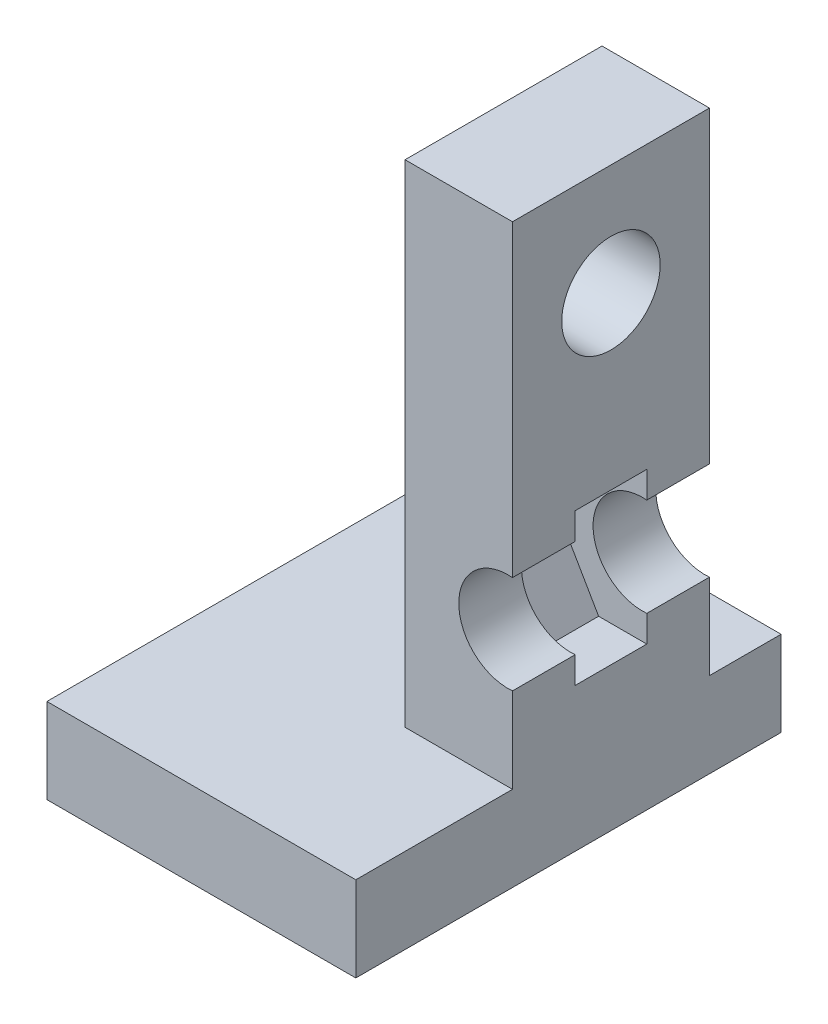
SolidWorks part; units mm, degrees
ref_plane "前基準面" through (0, 0, 0) normal (0, 0, 1) x (1, 0, 0)
ref_plane "上基準面" through (0, 0, 0) normal (0, 1, 0) x (1, 0, 0)
ref_plane "右基準面" through (0, 0, 0) normal (1, 0, 0) x (0, 0, -1)
sketch "草圖1" plane through (0, 0, 0) normal (0, 0, 1) x (1, 0, 0)
  line L0 (-0.3675, -59.7793) -> (-0.3675, -35.2793) construction
  line L1 (-11.8675, 4.6207) -> (11.1325, 4.6207)
  line L2 (-11.8675, 4.6207) -> (-11.8675, -59.7793)
  line L3 (-11.8675, -59.7793) -> (11.1325, -59.7793)
  line L4 (11.1325, 4.6207) -> (11.1325, -59.7793)
  line L5 (-7.6854, -31.0543) -> (6.9504, -39.5043) construction
  line L6 (9.3897, -35.2793) -> (4.5111, -26.8293)
  line L7 (4.5111, -26.8293) -> (-5.2461, -26.8293)
  line L8 (-5.2461, -26.8293) -> (-10.1247, -35.2793)
  line L9 (-10.1247, -35.2793) -> (-5.2461, -43.7293)
  line L10 (-5.2461, -43.7293) -> (4.5111, -43.7293)
  line L11 (4.5111, -43.7293) -> (9.3897, -35.2793)
  circle A0 centre (-0.3675, -35.2793) radius 8.45 construction
  dimension "D1" = 23
  dimension "D2" = 64.4
  dimension "D3" = 24.5
  dimension "D4" = 16.9
extrude "填料-伸長1" add sketch "草圖1" along normal blind 8
sketch "草圖3" plane through (0, 0, 8) normal (0, 0, 1) x (1, 0, 0)
  line L0 (-0.3675, -59.7793) -> (-0.3675, -35.2793) construction
  line L1 (-11.8675, 4.6207) -> (11.1325, 4.6207)
  line L2 (-11.8675, 4.6207) -> (-11.8675, -59.7793)
  line L3 (-11.8675, -59.7793) -> (11.1325, -59.7793)
  line L4 (11.1325, 4.6207) -> (11.1325, -59.7793)
  circle A0 centre (-0.3675, -35.2793) radius 5.5
extrude "填料-伸長2" add sketch "草圖3" along normal blind 7
sketch "草圖4" plane through (0, 0, 0) normal (0, 0, -1) x (-1, 0, 0)
  line L0 (0.3675, -59.7793) -> (0.3675, -35.2793) construction
  line L1 (-11.1325, 4.6207) -> (11.8675, 4.6207)
  line L2 (-11.1325, 4.6207) -> (-11.1325, -59.7793)
  line L3 (-11.1325, -59.7793) -> (11.8675, -59.7793)
  line L4 (11.8675, 4.6207) -> (11.8675, -59.7793)
  circle A0 centre (0.3675, -35.2793) radius 5.5
extrude "填料-伸長3" add sketch "草圖4" along normal blind 7
sketch "草圖5" plane through (11.1325, 0, 0) normal (1, 0, 0) x (0, 0, -1)
  line L0 (-4, -59.7793) -> (-4, -7.7793) construction
  line L1 (-15, -59.7793) -> (7, -59.7793) construction
  circle A0 centre (-4, -7.7793) radius 5.5
  dimension "D1" = 52
extrude "除料-伸長1" cut sketch "草圖5" against normal through all
sketch "草圖6" plane through (11.1325, 0, 0) normal (1, 0, 0) x (0, 0, -1)
  line L1 (-15, 4.6207) -> (7, 4.6207)
  line L2 (-15, 4.6207) -> (-15, -59.7793)
  line L3 (-15, -59.7793) -> (7, -59.7793)
  line L4 (7, 4.6207) -> (7, -59.7793)
extrude "除料-伸長2" cut sketch "草圖6" against normal blind 11
sketch "草圖8" plane through (0, -59.7793, 0) normal (0, -1, 0) x (1, 0, 0)
  line L0 (0.1325, -7) -> (0.1325, -15)
  line L1 (0.1325, -15) -> (-34.3675, -15)
  line L2 (-34.3675, -15) -> (-34.3675, 32.5)
  line L5 (-34.3675, 32.5) -> (0.1325, 32.5)
  line L7 (0.1325, 32.5) -> (0.1325, -7)
  dimension "D1" = 34.5
extrude "填料-伸長4" add sketch "草圖8" against normal blind 9.5
sketch "草圖9" plane through (0, -59.7793, 0) normal (0, -1, 0) x (1, 0, 0)
  line L0 (0.1325, -15) -> (-19.8675, -15) construction
  line L1 (-34.3675, -15) -> (0.1325, -15) construction
  line L2 (-19.8675, -15) -> (-19.8675, -3.5) construction
  circle A0 centre (-19.8675, -3.5) radius 5.5
  dimension "D1" = 11.5
  dimension "D2" = 20
extrude "除料-伸長3" cut sketch "草圖9" against normal blind 2.5
